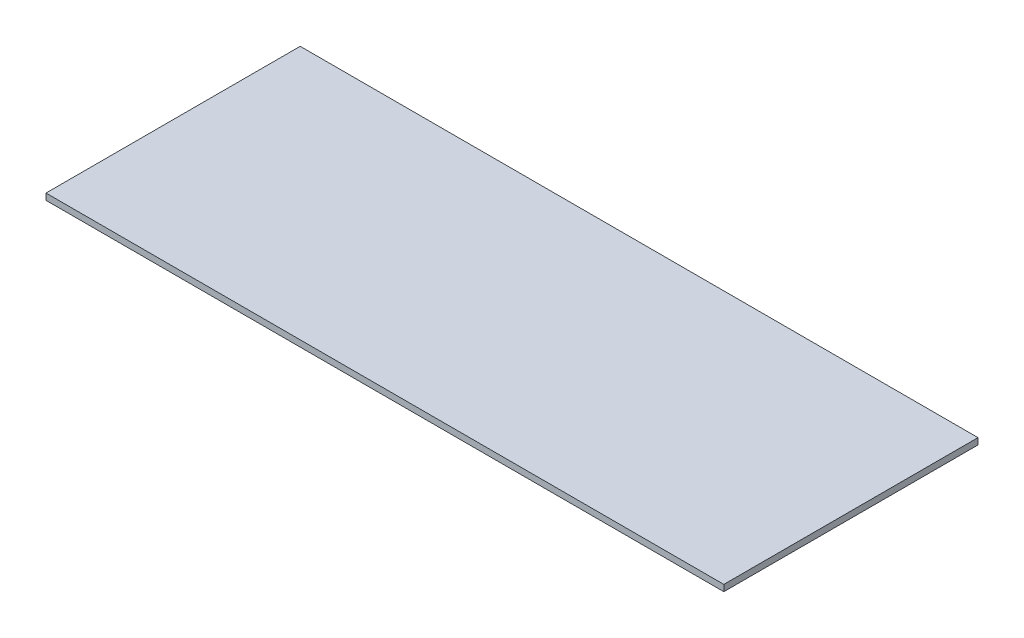
SolidWorks part; units mm, degrees
ref_plane "Спереди" through (0, 0, 0) normal (0, 0, 1) x (1, 0, 0)
ref_plane "Сверху" through (0, 0, 0) normal (0, 1, 0) x (1, 0, 0)
ref_plane "Справа" through (0, 0, 0) normal (1, 0, 0) x (0, 0, -1)
sketch "Эскиз1" plane through (0, 0, 0) normal (0, 1, 0) x (1, 0, 0)
  line L1 (-80, 30) -> (80, 30)
  line L2 (-80, 30) -> (-80, -30)
  line L3 (-80, -30) -> (80, -30)
  line L4 (80, 30) -> (80, -30)
  line L5 (-80, 30) -> (80, -30) construction
  line L6 (-80, -30) -> (80, 30) construction
  point P0 (0, 0)
extrude "Бобышка-Вытянуть1" add sketch "Эскиз1" along normal blind 1.5
